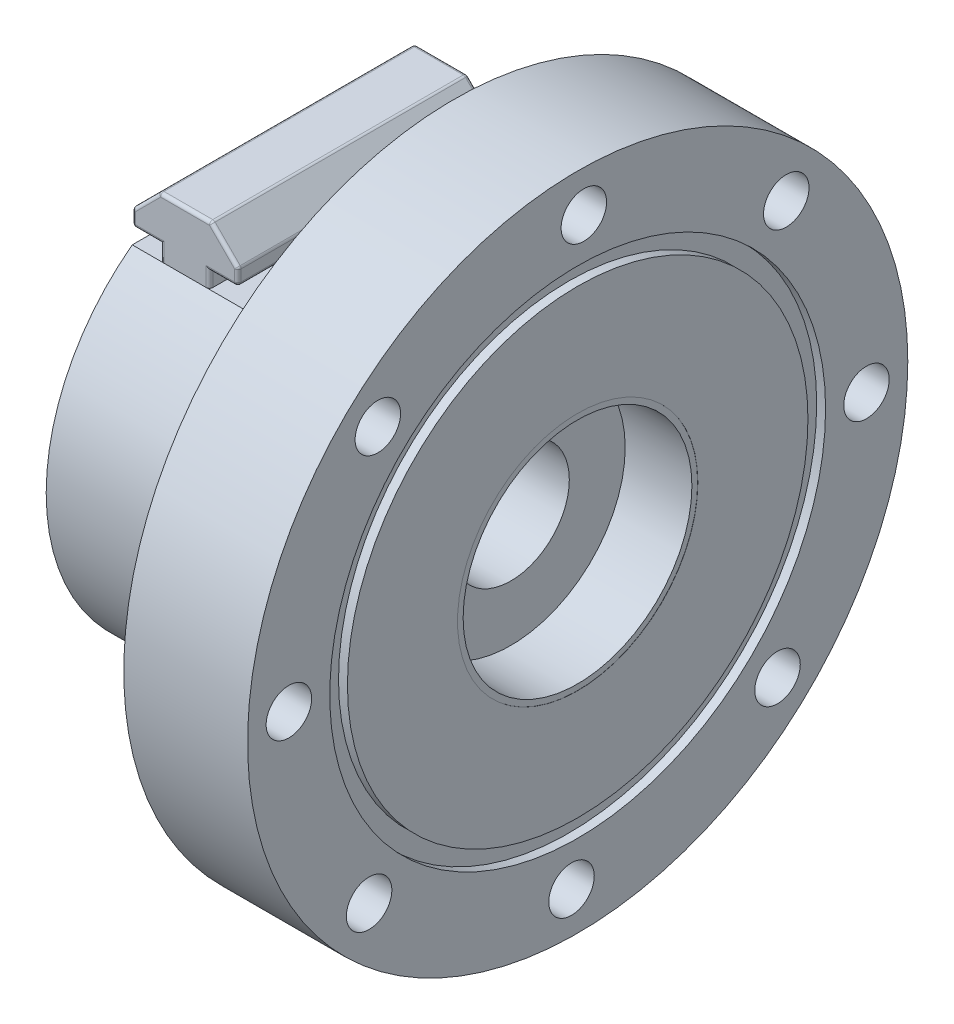
SolidWorks part; units mm, degrees
ref_plane "Front Plane" through (0, 0, 0) normal (0, 0, 1) x (1, 0, 0)
ref_plane "Top Plane" through (0, 0, 0) normal (0, 1, 0) x (1, 0, 0)
ref_plane "Right Plane" through (0, 0, 0) normal (1, 0, 0) x (0, 0, -1)
sketch "Main sketch" plane through (0, 0, 0) normal (0, 0, 1) x (1, 0, 0)
  line L0 (0, 9) -> (0, 20.075)
  line L1 (0, 20.075) -> (-8, 20.075)
  line L2 (-8, 20.075) -> (-8, 22.615)
  line L3 (-8, 33.02) -> (16.637, 33.02)
  line L4 (16.637, 33.02) -> (16.637, 50.8)
  line L5 (16.637, 50.8) -> (35.687, 50.8)
  line L6 (35.687, 50.8) -> (35.687, 38.1508)
  line L7 (35.687, 38.1508) -> (34.3154, 38.1508)
  line L8 (34.3154, 38.1508) -> (34.3154, 35.433)
  line L9 (34.3154, 35.433) -> (35.687, 35.433)
  line L10 (35.687, 35.433) -> (35.687, 18.4912)
  line L11 (35.687, 18.4912) -> (35.6616, 18.4912)
  line L12 (35.6616, 18.4912) -> (35.6616, 17.6022)
  line L13 (35.6616, 17.6022) -> (25.4, 17.6022)
  line L14 (25.4, 17.6022) -> (25.4, 9)
  line L15 (25.4, 9) -> (0, 9)
  line L16 (0, 0) -> (0, 9) construction
  line L17 (-8, 22.615) -> (-13.08, 22.615)
  line L18 (-13.08, 22.615) -> (-13.08, 33.02)
  line L19 (-13.08, 33.02) -> (-8, 33.02)
  point P20 (35.0012, 35.433)
  dimension "D1" = 9
  dimension "D2" = 20.075
  dimension "D4" = 17.6022
  dimension "D5" = 8
  dimension "D6" = 50.8
  dimension "D7" = 18.4912
  dimension "D11" = 25.4
  dimension "D12" = 10.2616
  dimension "D13" = 33.02
  dimension "D14" = 19.05
  dimension "D10" = 1.3716
  dimension "D15" = 5.08
  dimension "D16" = 2.54
  dimension "D3" = 180
  dimension "D17" = 0.0254
  dimension "D18" = 0.0254
  dimension "D8" = 38.1508
  dimension "D9" = 2.7178
ref_axis "Axis1" through (71.9501, 0, 0) along (-1, 0, 0)
revolve "Revolve1" add sketch "Main sketch" angle 360 about axis through (71.9501, 0, 0) along (-1, 0, 0)
sketch "Sketch2" plane through (35.687, 0, 0) normal (1, 0, 0) x (0, 0, -1)
  circle A0 centre (0, 0) radius 44.45 construction
  point P0 (0, 0)
  point P3 (-44.4399, 0.9486)
  point P4 (-32.0945, -30.753)
  point P7 (-0.9486, -44.4399)
  point P8 (30.753, -32.0945)
  point P9 (44.4399, -0.9486)
  point P10 (32.0945, 30.753)
  point P11 (0.9486, 44.4399)
  point P12 (-30.753, 32.0945)
  point P13 (0, 0)
  point P16 (0, 0)
  dimension "D2" = 88.9
  dimension "D1" = 8
hole_wizard "M6 Clearance Hole1" positions "Sketch2" profile "Sketch3" hole size "M6" standard "ISO" end condition through all
sketch "Sketch3" plane through (35.687, 0, 0) normal (0, 1, 0) x (0, 0, -1)
  line L0 (0, 0) -> (0, 48.767)
  line L1 (0, 48.767) -> (3.5, 48.767)
  line L2 (3.5, 48.767) -> (3.5, 0)
  line L5 (3.5, 0) -> (0, 0)
  line L11 (0, -6.35) -> (0, 107.95) construction
  dimension "Thru Hole Dia." = 7
  dimension "Thru Hole Depth" = 48.767
ref_plane "Plane1" through (0, 0, 33.02) normal (0, 0, 1) x (1, 0, 0)
ref_plane "Plane2" through (0, 33.02, 0) normal (0, 1, 0) x (1, 0, 0)
ref_plane "Plane3" through (0, 0, -33.02) normal (0, 0, -1) x (-1, 0, 0)
sketch "Sketch4" plane through (0, 33.02, 0) normal (0, 1, 0) x (1, 0, 0)
  line L0 (-13.08, -33.02) -> (16.637, -33.02) construction
  line L1 (16.637, 33.02) -> (16.637, -33.02) construction
  line L2 (16.637, 33.02) -> (-13.08, 33.02) construction
  line L4 (-13.08, -33.02) -> (16.637, -33.02)
  line L5 (16.637, 33.02) -> (16.637, -33.02)
  line L6 (16.637, 33.02) -> (-13.08, 33.02)
  line L8 (-13.08, 33.02) -> (-13.08, -33.02) construction
  line L9 (-13.08, 33.02) -> (-13.08, -33.02)
extrude "Cut-Extrude1" cut sketch "Sketch4" against normal blind 6.5786
ref_plane "Plane4" through (0, 0, -19.7781) normal (0, 0, 1) x (1, 0, 0)
ref_plane "Plane5" through (0, 0, 19.7781) normal (0, 0, -1) x (-1, 0, 0)
sketch "Sketch5" plane through (0, 0, 19.7781) normal (0, 0, -1) x (-1, 0, 0)
  line L0 (13.08, 26.4414) -> (-16.637, 26.4414) construction
  line L1 (13.08, 26.4414) -> (-16.637, 26.4414)
  line L2 (1.1912, 26.4414) -> (1.1912, 28.8684)
  line L3 (1.1912, 28.8684) -> (-3.176, 28.8684)
  line L4 (-3.176, 28.8684) -> (-3.176, 31.3274)
  line L5 (-3.176, 31.3274) -> (0.9888, 35.4922)
  line L6 (0.9888, 35.4922) -> (8.9152, 35.4922)
  line L7 (4.952, 35.4922) -> (4.952, 26.4414) construction
  line L8 (8.7128, 26.4414) -> (1.1912, 26.4414)
  line L9 (8.7128, 26.4414) -> (8.7128, 28.8684)
  line L10 (8.7128, 28.8684) -> (13.08, 28.8684)
  line L11 (13.08, 28.8684) -> (13.08, 31.3274)
  line L12 (13.08, 31.3274) -> (8.9152, 35.4922)
  line L14 (13.08, -33.02) -> (13.08, 26.4414) construction
  dimension "D1" = 3.7608
  dimension "D2" = 2.427
  dimension "D3" = 135
  dimension "D4" = 6.6238
  dimension "D5" = 8.128
  dimension "D6" = 7.9264
extrude "Boss-Extrude1" add sketch "Sketch5" along normal up to surface (39.5562 mm away) contours L7 L6 L5 L4 L3 L2 L8 | L6 L7 L1 L9 L10 L11 L12 up to plane "Plane4"
fillet "Fillet1" radius 0.508 24 edges at (-4.952, 35.4922, -19.7781) (-1.1912, 27.6549, -19.7781) (-1.1912, 27.6549, 19.7781) (3.176, 30.0979, -19.7781) (3.176, 30.0979, 19.7781) (0.9924, 28.8684, -19.7781) (0.9924, 28.8684, 19.7781) (1.0936, 33.4098, -19.7781) (1.0936, 33.4098, 19.7781) (-4.952, 35.4922, 19.7781) (-10.8964, 28.8684, -19.7781) (-10.8964, 28.8684, 19.7781) (-8.7128, 27.6549, -19.7781) (-8.7128, 27.6549, 19.7781) (-10.9976, 33.4098, -19.7781) (-8.9152, 35.4922, 0) (-10.9976, 33.4098, 19.7781) (-13.08, 30.0979, -19.7781) (-13.08, 30.0979, 19.7781) (-0.9888, 35.4922, 0) (3.176, 31.3274, 0) (3.176, 28.8684, 0) (-13.08, 31.3274, 0) (-13.08, 28.8684, 0)
mirror "Mirror1" about plane through (0, 0, 0) normal (0, 1, 0) of "Cut-Extrude1", "Boss-Extrude1", "Fillet1"
equation "\"Shaft_OD\"= 17mm'outer diameter of shaft"
equation "\"O_Ring_ID\"= 2.864in"
equation "\"O_Ring_CS\"= .070in'cross section"
equation "\"Bearing_OD\"= 40.15mm"
equation "\"Bearing_Depth\"= 8mm'depth bearing goes into the casing"
equation "\"Stationary_Face_Seal_OD\"= 1.386in"
equation "\"Flange_Dia\"= 4in"
equation "\"Screw_Dia\"= 6mm"
equation "\"Seal_Space\"= .3in"
equation "\"D1@Main sketch\"=\"Shaft_OD\" / 2 + .5mm"
equation "\"D2@Main sketch\" = \"Bearing_OD\" / 2"
equation "\"D4@Main sketch\" = \"Stationary_Face_Seal_OD\" / 2"
equation "\"D5@Main sketch\" = \"Bearing_Depth\""
equation "\"D6@Main sketch\" = \"Flange_Dia\" / 2"
equation "\"Seal_Area_Dia\"= 37mm"
equation "\"D7@Main sketch\"=\"Seal_space_Dia\"/2"
equation "\"Face_Seal_Height\"= 0.404in"
equation "\"D12@Main sketch\" = \"Face_Seal_Height\""
equation "\"Housing_OR\"= 1.3in'Outer radius of housing"
equation "\"D10@Main sketch\"=.054"
equation "\"D2@Sketch2\"=\"Flange_Dia\"-\"Screw_offset\""
equation "\"Screw_offset\"= .5in'offset of screws from flange OD."
equation "\"Seal_space_Dia\"= \"Stationary_Face_Seal_OD\" + .07'diameter of the space for the face seal"
equation "\"D8@Main sketch\"=(\"O_Ring_ID\"+2*\"O_Ring_CS\")/2"
equation "\"Groove_width\"=0.107"
equation "\"D9@Main sketch\"=\"Groove_width\""
